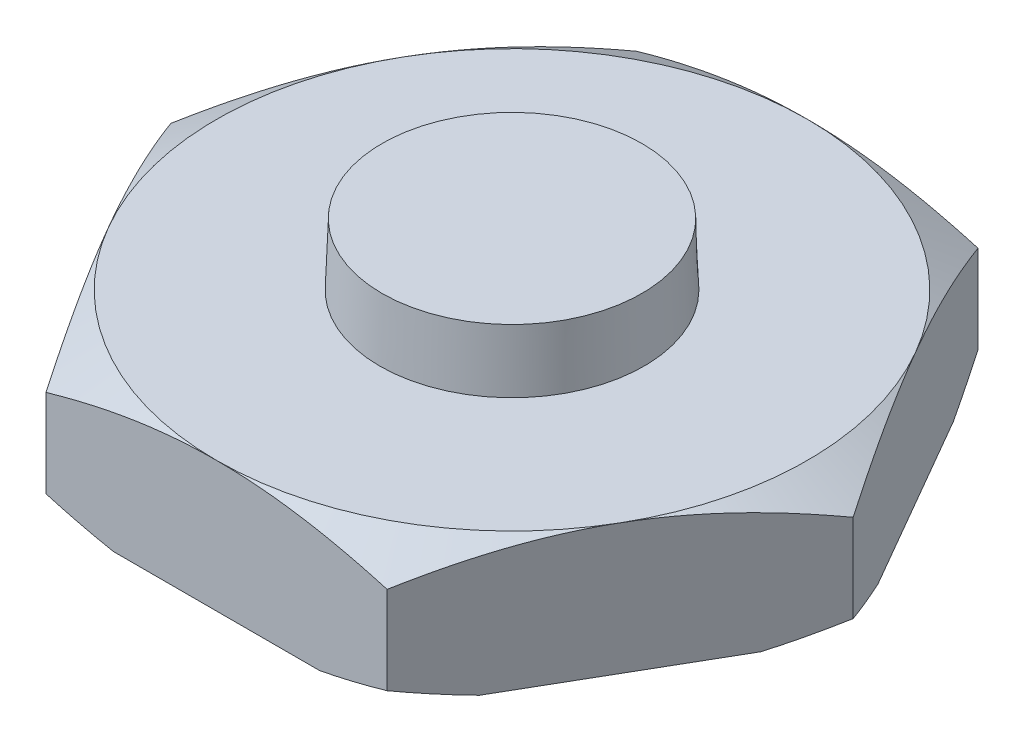
SolidWorks part; units mm, degrees
ref_plane "Front Plane" through (0, 0, 0) normal (0, 0, 1) x (1, 0, 0)
ref_plane "Top Plane" through (0, 0, 0) normal (0, 1, 0) x (1, 0, 0)
ref_plane "Right Plane" through (0, 0, 0) normal (1, 0, 0) x (0, 0, -1)
ref_plane "Plane1" through (0, 0, 0) normal (0, 0, 1) x (1, 0, 0)
sketch "Sketch1" plane through (0, 0, 0) normal (0, 0, 1) x (1, 0, 0)
  line L0 (0, 34.0386) -> (5.5795, 34.0386)
  line L1 (5.5795, 34.0386) -> (5.5795, 14.2396)
  line L2 (5.5795, 14.2396) -> (5.6822, 11.4036)
  line L3 (5.6822, 11.4036) -> (12.7, 11.4036)
  line L4 (12.7, 11.4036) -> (17.9334, 8.3821)
  line L5 (17.9334, 8.3821) -> (13.45, 5.7936)
  line L6 (13.45, 5.7936) -> (0, 5.7936)
  line L7 (0, 5.7936) -> (0, 34.0386)
  line L8 (0, 5.7936) -> (0, 34.0386) construction
revolve "Revolve1" add sketch "Sketch1" angle 360 about L8
ref_plane "Plane2" through (0, 11.4036, 0) normal (0, 1, 0) x (1, 0, 0)
sketch "Sketch2" plane through (0, 11.4036, 0) normal (0, 1, 0) x (1, 0, 0)
  line L0 (23.734, -20.3506) -> (23.734, 18.7347)
  line L1 (23.734, 18.7347) -> (-23.431, 18.7347)
  line L2 (-23.431, 18.7347) -> (-23.431, -20.3506)
  line L3 (-23.431, -20.3506) -> (23.734, -20.3506)
  line L4 (14.6647, 0) -> (7.3323, 12.7)
  line L5 (7.3323, 12.7) -> (-7.3323, 12.7)
  line L6 (-7.3323, 12.7) -> (-14.6647, 0)
  line L7 (-14.6647, 0) -> (-7.3323, -12.7)
  line L8 (-7.3323, -12.7) -> (7.3323, -12.7)
  line L9 (7.3323, -12.7) -> (14.6647, 0)
extrude "Cut-Extrude1" cut sketch "Sketch2" against normal blind 5.61
ref_plane "Plane3" through (0, 14.0616, 0) normal (0, 1, 0) x (1, 0, 0)
sketch "Sketch3" plane through (0, 14.0616, 0) normal (0, 1, 0) x (1, 0, 0)
  line L0 (-20, -20) -> (20, -20)
  line L1 (20, -20) -> (20, 20)
  line L2 (20, 20) -> (-20, 20)
  line L3 (-20, 20) -> (-20, -20)
extrude "Cut-Extrude2" cut sketch "Sketch3" along normal blind 50
